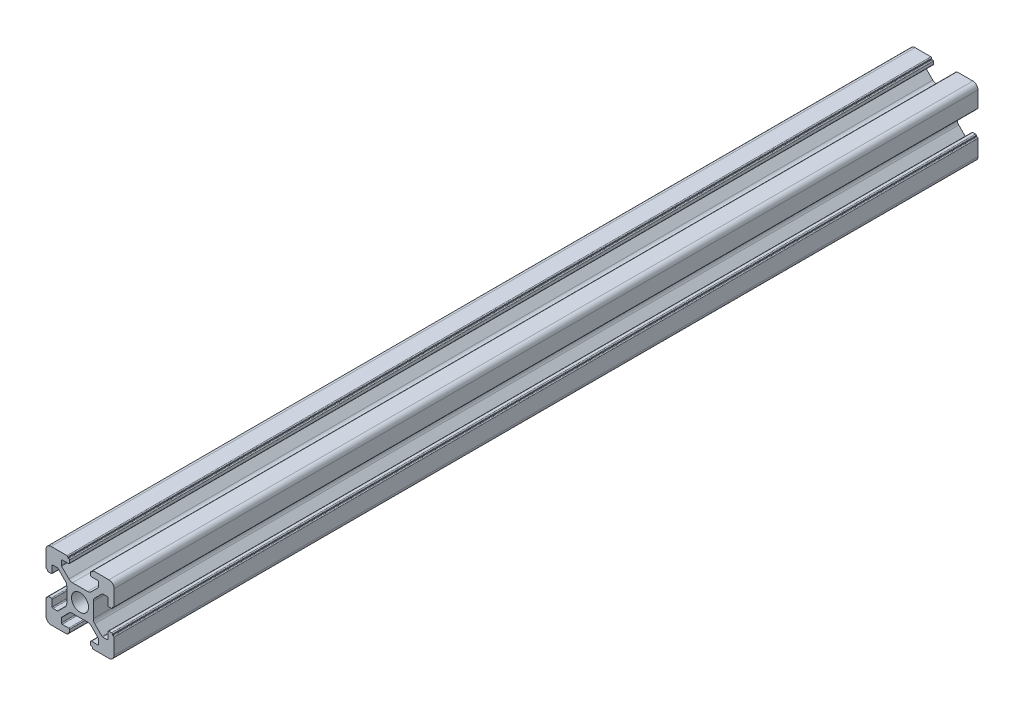
SolidWorks part; units mm, degrees
material "1060 Alloy"
ref_plane "前视基准面" through (0, 0, 0) normal (0, 0, 1) x (1, 0, 0)
ref_plane "上视基准面" through (0, 0, 0) normal (0, 1, 0) x (1, 0, 0)
ref_plane "右视基准面" through (0, 0, 0) normal (1, 0, 0) x (0, 0, -1)
sketch "草图1" plane through (0, 0, 0) normal (0, 0, 1) x (1, 0, 0)
  line L0 (0, 0) -> (0, 5.5) construction
  line L1 (-8.5023, -10.0023) -> (-3.85, -10.0023)
  line L2 (-10.0023, -8.5023) -> (-10.0023, -3.85)
  line L3 (-8.5023, 10.0023) -> (-3.85, 10.0023)
  line L4 (10.0023, -8.5023) -> (10.0023, -3.85)
  line L5 (-10.0023, -10.0023) -> (10.0023, 10.0023) construction
  line L6 (-10.0023, 10.0023) -> (10.0023, -10.0023) construction
  line L7 (-2.218, -3.9) -> (2.218, -3.9)
  line L8 (-3.9, -2.218) -> (-3.9, 2.218)
  line L9 (-2.218, 3.9) -> (2.218, 3.9)
  line L10 (3.9, -2.218) -> (3.9, 2.218)
  line L11 (-3.9, -3.9) -> (3.9, 3.9) construction
  line L12 (-3.9, 3.9) -> (3.9, -3.9) construction
  line L13 (-5.25, -8.2) -> (-3.35, -8.2)
  line L14 (-8.2, -5.25) -> (-8.2, -3.35)
  line L15 (-5.25, 8.2) -> (-3.35, 8.2)
  line L16 (8.2, -5.25) -> (8.2, -3.35)
  line L17 (-8.2, -8.2) -> (8.2, 8.2) construction
  line L18 (-8.2, 8.2) -> (8.2, -8.2) construction
  line L19 (-7.95, 5.5) -> (-6.6642, 5.5)
  line L20 (0, 0) -> (5.5, 0) construction
  line L23 (-5.5, 7.95) -> (-5.5, 6.6642)
  line L26 (0, 0) -> (-0.5303, 0.5303)
  line L27 (3.2787, 4.3393) -> (5.4268, 6.4874)
  line L28 (0, 0) -> (0.5303, -0.5303)
  line L29 (5.5, 6.6642) -> (5.5, 7.95)
  line L30 (4.3393, 3.2787) -> (6.4874, 5.4268)
  line L31 (6.6642, 5.5) -> (7.95, 5.5)
  line L32 (4.3393, -3.2787) -> (6.4874, -5.4268)
  line L33 (3.2787, -4.3393) -> (5.4268, -6.4874)
  line L34 (-3.2787, -4.3393) -> (-5.4268, -6.4874)
  line L35 (-4.3393, -3.2787) -> (-6.4874, -5.4268)
  line L36 (-4.3393, 3.2787) -> (-6.4874, 5.4268)
  line L37 (-3.2787, 4.3393) -> (-5.4268, 6.4874)
  line L38 (3.1, -8.45) -> (3.1, -9.2523)
  line L39 (8.45, 3.1) -> (9.2523, 3.1)
  line L40 (-5.5, -6.6642) -> (-5.5, -7.95)
  line L41 (-6.6642, -5.5) -> (-7.95, -5.5)
  line L42 (5.5, -6.6642) -> (5.5, -7.95)
  line L43 (6.6642, -5.5) -> (7.95, -5.5)
  line L44 (9.2523, -3.1) -> (8.45, -3.1)
  line L46 (10.0023, 3.85) -> (10.0023, 8.5023)
  line L47 (8.2, 3.35) -> (8.2, 5.25)
  line L48 (-3.1, -9.2523) -> (-3.1, -8.45)
  line L49 (-8.45, -3.1) -> (-9.2523, -3.1)
  line L50 (-9.2523, 3.1) -> (-8.45, 3.1)
  line L51 (-3.1, 8.45) -> (-3.1, 9.2523)
  line L52 (3.1, 9.2523) -> (3.1, 8.45)
  line L53 (3.85, 10.0023) -> (8.5023, 10.0023)
  line L54 (3.35, 8.2) -> (5.25, 8.2)
  line L55 (-10.0023, 3.85) -> (-10.0023, 8.5023)
  line L56 (-8.2, 3.35) -> (-8.2, 5.25)
  line L57 (3.35, -8.2) -> (5.25, -8.2)
  line L58 (3.85, -10.0023) -> (8.5023, -10.0023)
  line L59 (9.7523, -3.6) -> (9.5023, -3.6)
  line L61 (9.7523, 3.6) -> (9.5023, 3.6)
  line L62 (9.5023, -3.6) -> (9.5023, -3.35)
  line L63 (3.6, -9.7523) -> (3.6, -9.5023)
  line L64 (3.35, -9.5023) -> (3.6, -9.5023)
  line L65 (9.5023, 3.35) -> (9.5023, 3.6)
  line L66 (-3.6, -9.5023) -> (-3.35, -9.5023)
  line L67 (-3.6, -9.7523) -> (-3.6, -9.5023)
  line L68 (-9.7523, -3.6) -> (-9.5023, -3.6)
  line L69 (-9.5023, -3.35) -> (-9.5023, -3.6)
  line L70 (-9.5023, 3.6) -> (-9.5023, 3.35)
  line L71 (-9.7523, 3.6) -> (-9.5023, 3.6)
  line L72 (-3.6, 9.7523) -> (-3.6, 9.5023)
  line L73 (-3.35, 9.5023) -> (-3.6, 9.5023)
  line L74 (3.6, 9.5023) -> (3.35, 9.5023)
  line L75 (3.6, 9.7523) -> (3.6, 9.5023)
  circle A0 centre (0, 0) radius 2.5
  arc A1 (10.0023, 8.5023) -> (8.5023, 10.0023) centre (8.5023, 8.5023) ccw
  arc A2 (8.5023, -10.0023) -> (10.0023, -8.5023) centre (8.5023, -8.5023) ccw
  arc A3 (-10.0023, -8.5023) -> (-8.5023, -10.0023) centre (-8.5023, -8.5023) ccw
  arc A4 (-10.0023, 8.5023) -> (-8.5023, 10.0023) centre (-8.5023, 8.5023) cw
  arc A5 (-9.5023, -3.35) -> (-9.2523, -3.1) centre (-9.2523, -3.35) cw
  arc A6 (-9.7523, -3.6) -> (-10.0023, -3.85) centre (-9.7523, -3.85) ccw
  arc A7 (-8.45, -3.1) -> (-8.2, -3.35) centre (-8.45, -3.35) cw
  arc A8 (-7.95, -5.5) -> (-8.2, -5.25) centre (-7.95, -5.25) cw
  arc A9 (-6.4874, -5.4268) -> (-6.6642, -5.5) centre (-6.6642, -5.25) cw
  arc A10 (-5.4268, -6.4874) -> (-5.5, -6.6642) centre (-5.25, -6.6642) ccw
  arc A11 (-5.5, -7.95) -> (-5.25, -8.2) centre (-5.25, -7.95) ccw
  arc A12 (-3.6, -9.7523) -> (-3.85, -10.0023) centre (-3.85, -9.7523) cw
  arc A13 (-3.35, -9.5023) -> (-3.1, -9.2523) centre (-3.35, -9.2523) ccw
  arc A14 (-3.1, -8.45) -> (-3.35, -8.2) centre (-3.35, -8.45) ccw
  arc A15 (3.1, -8.45) -> (3.35, -8.2) centre (3.35, -8.45) cw
  arc A16 (5.5, -7.95) -> (5.25, -8.2) centre (5.25, -7.95) cw
  arc A17 (5.4268, -6.4874) -> (5.5, -6.6642) centre (5.25, -6.6642) cw
  arc A18 (6.4874, -5.4268) -> (6.6642, -5.5) centre (6.6642, -5.25) ccw
  arc A19 (7.95, -5.5) -> (8.2, -5.25) centre (7.95, -5.25) ccw
  arc A20 (8.45, -3.1) -> (8.2, -3.35) centre (8.45, -3.35) ccw
  arc A21 (9.5023, -3.35) -> (9.2523, -3.1) centre (9.2523, -3.35) ccw
  arc A22 (9.7523, -3.6) -> (10.0023, -3.85) centre (9.7523, -3.85) cw
  arc A23 (3.35, -9.5023) -> (3.1, -9.2523) centre (3.35, -9.2523) cw
  arc A24 (3.6, -9.7523) -> (3.85, -10.0023) centre (3.85, -9.7523) ccw
  arc A25 (7.95, 5.5) -> (8.2, 5.25) centre (7.95, 5.25) cw
  arc A26 (8.2, 3.35) -> (8.45, 3.1) centre (8.45, 3.35) ccw
  arc A27 (9.5023, 3.35) -> (9.2523, 3.1) centre (9.2523, 3.35) cw
  arc A28 (9.7523, 3.6) -> (10.0023, 3.85) centre (9.7523, 3.85) ccw
  arc A29 (6.6642, 5.5) -> (6.4874, 5.4268) centre (6.6642, 5.25) ccw
  arc A30 (5.4268, 6.4874) -> (5.5, 6.6642) centre (5.25, 6.6642) ccw
  arc A31 (5.5, 7.95) -> (5.25, 8.2) centre (5.25, 7.95) ccw
  arc A32 (3.1, 8.45) -> (3.35, 8.2) centre (3.35, 8.45) ccw
  arc A33 (3.6, 9.7523) -> (3.85, 10.0023) centre (3.85, 9.7523) cw
  arc A34 (3.35, 9.5023) -> (3.1, 9.2523) centre (3.35, 9.2523) ccw
  arc A35 (-9.7523, 3.6) -> (-10.0023, 3.85) centre (-9.7523, 3.85) cw
  arc A36 (-9.5023, 3.35) -> (-9.2523, 3.1) centre (-9.2523, 3.35) ccw
  arc A37 (-8.45, 3.1) -> (-8.2, 3.35) centre (-8.45, 3.35) ccw
  arc A38 (-8.2, 5.25) -> (-7.95, 5.5) centre (-7.95, 5.25) cw
  arc A39 (-6.4874, 5.4268) -> (-6.6642, 5.5) centre (-6.6642, 5.25) ccw
  arc A40 (-5.4268, 6.4874) -> (-5.5, 6.6642) centre (-5.25, 6.6642) cw
  arc A41 (-5.5, 7.95) -> (-5.25, 8.2) centre (-5.25, 7.95) cw
  arc A42 (-3.1, 8.45) -> (-3.35, 8.2) centre (-3.35, 8.45) cw
  arc A43 (-3.1, 9.2523) -> (-3.35, 9.5023) centre (-3.35, 9.2523) ccw
  arc A44 (-3.6, 9.7523) -> (-3.85, 10.0023) centre (-3.85, 9.7523) ccw
  arc A45 (-4.3393, 3.2787) -> (-3.9, 2.218) centre (-5.4, 2.218) cw
  arc A46 (-3.2787, 4.3393) -> (-2.218, 3.9) centre (-2.218, 5.4) ccw
  arc A47 (3.2787, 4.3393) -> (2.218, 3.9) centre (2.218, 5.4) cw
  arc A48 (4.3393, 3.2787) -> (3.9, 2.218) centre (5.4, 2.218) ccw
  arc A49 (4.3393, -3.2787) -> (3.9, -2.218) centre (5.4, -2.218) cw
  arc A50 (3.2787, -4.3393) -> (2.218, -3.9) centre (2.218, -5.4) ccw
  arc A51 (-4.3393, -3.2787) -> (-3.9, -2.218) centre (-5.4, -2.218) ccw
  arc A52 (-2.218, -3.9) -> (-3.2787, -4.3393) centre (-2.218, -5.4) ccw
  point P0 (0, 0)
  point P7 (10.0023, 0)
  point P62 (0, 0)
  point P76 (0, 0)
  point P92 (-8.2, -5.5)
  point P99 (0, 0)
  point P106 (-5.5, -8.2)
  point P117 (5.5, -8.2)
  point P124 (8.2, -5.5)
  point P137 (8.2, 5.5)
  point P140 (8.2, 3.1)
  point P147 (6.5607, 5.5)
  point P152 (5.5, 8.2)
  point P167 (-8.2, 5.5)
  point P174 (-5.5, 8.2)
  dimension "D1" = 1.5
  dimension "D5" = 0.25
  dimension "D6" = 1.5
  dimension "D2" = 4
  dimension "D3" = 4
  dimension "D4" = 4
extrude "凸台-拉伸1" add sketch "草图1" along normal blind 254 contours A52 L7 A50 L33 A17 L42 A16 L57 A15 L38 A23 L64 L63 A24 L58 A2 L4 A22 L59 L62 A21 L44 A20 L16 A19 L43 A18 L32 A49 L10 A48 L30 A29 L31 A25 L47 A26 L39 A27 L65 L61 A28 L46 A1 L53 A33 L75 L74 A34 L52 A32
ref_plane "Plane1" through (0, 0, 127) normal (0, 0, 1) x (1, 0, 0)
